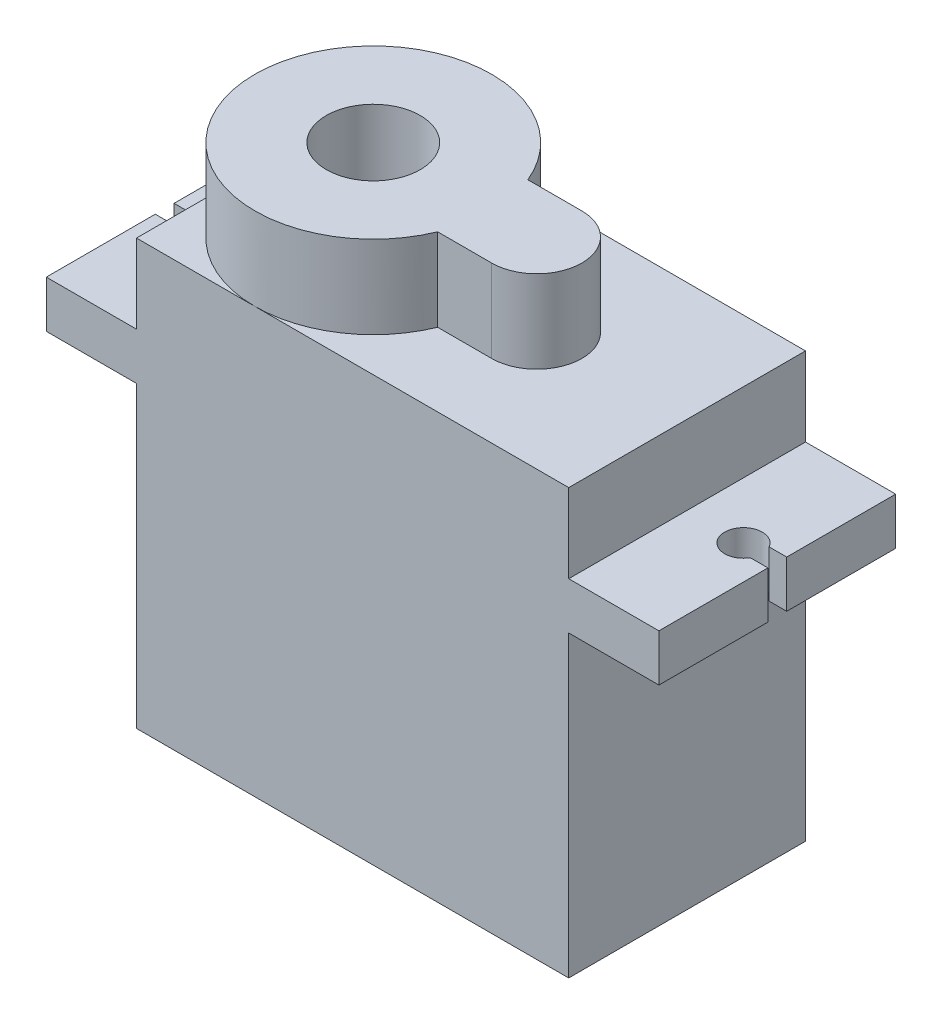
SolidWorks part; units mm, degrees
ref_plane "Alzado" through (0, 0, 0) normal (0, 0, 1) x (1, 0, 0)
ref_plane "Planta" through (0, 0, 0) normal (0, 1, 0) x (1, 0, 0)
ref_plane "Vista lateral" through (0, 0, 0) normal (1, 0, 0) x (0, 0, -1)
sketch "Croquis1" plane through (0, 0, 0) normal (0, 0, 1) x (1, 0, 0)
  line L0 (11.5, 0) -> (-11.5, 0)
  line L1 (-11.5, 0) -> (-11.5, 15.9)
  line L2 (-11.5, 15.9) -> (-16.3, 15.9)
  line L3 (-16.3, 15.9) -> (-16.3, 18.4)
  line L4 (-16.3, 18.4) -> (-11.5, 18.4)
  line L5 (-11.5, 18.4) -> (-11.5, 22.6)
  line L6 (-11.5, 22.6) -> (11.5, 22.6)
  line L8 (0, 35.0828) -> (0, -5.7212) construction
  line L9 (11.5, 0) -> (11.5, 15.9)
  line L10 (11.5, 15.9) -> (16.3, 15.9)
  line L11 (16.3, 15.9) -> (16.3, 18.4)
  line L12 (16.3, 18.4) -> (11.5, 18.4)
  line L13 (11.5, 18.4) -> (11.5, 22.6)
  dimension "D1" = 23
  dimension "D2" = 15.9
  dimension "D3" = 2.5
  dimension "D4" = 4.2
  dimension "D5" = 4.8
  dimension "D6" = 4.8
extrude "Saliente-Extruir1" add sketch "Croquis1" along normal blind 12.6 contours L1 L2 L3 L4 L5 L6 L13 L12 L11 L10 L9 L0
sketch "Croquis2" plane through (0, 18.4, 0) normal (0, 1, 0) x (1, 0, 0)
  line L0 (-16.3, -12.6) -> (-16.3, -6.8) construction
  line L1 (-16.3, -12.6) -> (-16.3, 0) construction
  line L2 (-16.3, -6.3) -> (16.3, -6.3) construction
  line L3 (16.3, -12.6) -> (16.3, 0) construction
  line L4 (-16.3, 0) -> (-16.3, -5.8) construction
  line L5 (-16.3, -6.8) -> (-15.366, -6.8)
  line L6 (-16.3, -5.8) -> (-15.366, -5.8)
  line L7 (0, 0) -> (0, -12.6) construction
  line L8 (-11.5, -12.6) -> (11.5, -12.6) construction
  line L9 (-16.3, -6.8) -> (-16.3, -5.8)
  line L10 (-15.366, -5.8) -> (-15.366, -6.8)
  line L11 (15.366, -5.8) -> (15.366, -6.8)
  line L12 (16.3, -5.8) -> (15.366, -5.8)
  line L13 (16.3, -6.8) -> (16.3, -5.8)
  line L14 (16.3, -6.8) -> (15.366, -6.8)
  line L15 (-13.5, -6.3) -> (-13.5, -4.3984) construction
  line L16 (-11.503, -6.3) -> (-11.5, -4.3984) construction
  line L17 (-11.5, -12.6) -> (-11.5, 0) construction
  circle A0 centre (-14.5, -6.3) radius 1
  circle A1 centre (14.5, -6.3) radius 1
  point P12 (-14.5, -6.3)
  dimension "D4" = 1
  dimension "D1" = 5.8
  dimension "D2" = 2
  dimension "D3" = 1.8
extrude "Cortar-Extruir2" cut sketch "Croquis2" against normal blind 2.5
sketch "Croquis4" plane through (0, 22.6, 0) normal (0, 1, 0) x (1, 0, 0)
  line L0 (-11.5, -6.3) -> (-5.2, -6.3) construction
  line L1 (-11.5, -12.6) -> (-11.5, 0) construction
  line L2 (-5.2, -6.3) -> (3.5, -6.3) construction
  line L4 (-1.3, -8.7) -> (3.5, -8.7)
  line L5 (-1.3, -8.7) -> (-1.3, -3.9)
  line L6 (-1.3, -3.9) -> (3.5, -3.9)
  line L7 (3.5, -8.7) -> (3.5, -3.9)
  line L8 (-1.3, -8.7) -> (3.5, -3.9) construction
  line L9 (-1.3, -3.9) -> (3.5, -8.7) construction
  circle A0 centre (-5.2, -6.3) radius 6.3
  circle A1 centre (3.5, -6.3) radius 2.4
  circle A2 centre (-5.2, -6.3) radius 2.5
  point P7 (1.1, -6.3)
  point P8 (1.1, -6.3)
  dimension "D2" = 12.6
  dimension "D4" = 4.8
  dimension "D5" = 5
  dimension "D1" = 6.3
  dimension "D3" = 8.7
extrude "Saliente-Extruir4" add sketch "Croquis4" along normal blind 4.4 contours A0 L4 L5 L6 A2 | L7 A1 | L7 A1 | A1 A0 L4 | A1 L6 A0 | L4 A0 L6 L5
